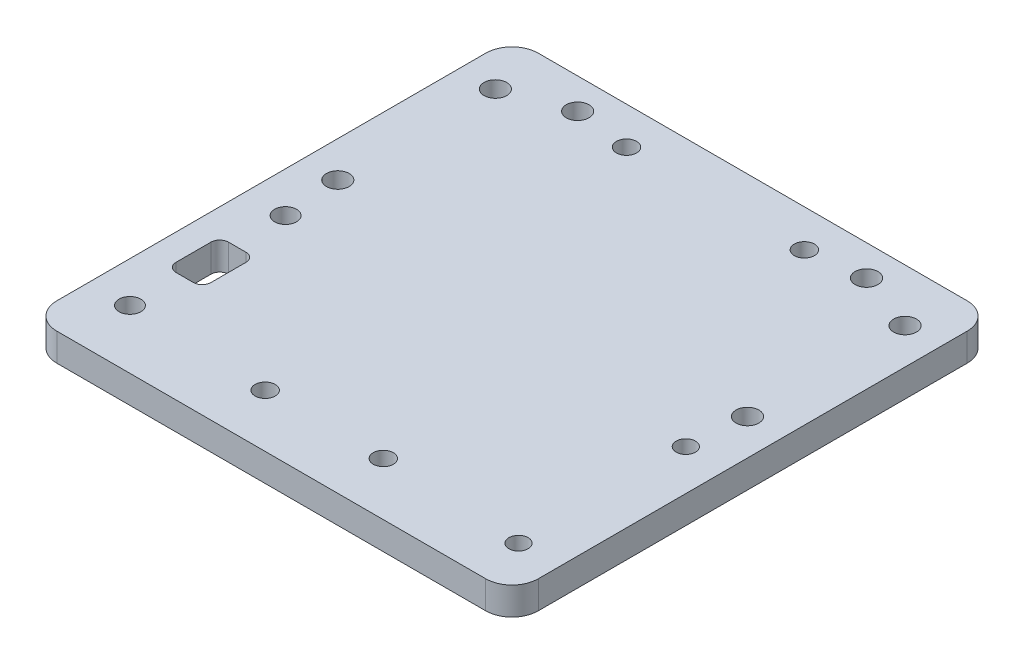
SolidWorks part; units mm, degrees
ref_plane "Front Plane" through (0, 0, 0) normal (0, 0, 1) x (1, 0, 0)
ref_plane "Top Plane" through (0, 0, 0) normal (0, 1, 0) x (1, 0, 0)
ref_plane "Right Plane" through (0, 0, 0) normal (1, 0, 0) x (0, 0, -1)
sketch "Sketch1" plane through (0, 0, 0) normal (0, 1, 0) x (1, 0, 0)
  line L1 (-27.5, 27.5) -> (27.5, 27.5)
  line L2 (-27.5, 27.5) -> (-27.5, -27.5)
  line L3 (-27.5, -27.5) -> (27.5, -27.5)
  line L4 (27.5, 27.5) -> (27.5, -27.5)
  line L5 (-27.5, 27.5) -> (27.5, -27.5) construction
  line L6 (-27.5, -27.5) -> (27.5, 27.5) construction
  point P0 (0, 0)
  dimension "D1" = 55
  dimension "D2" = 55
extrude "Boss-Extrude1" add sketch "Sketch1" along normal blind 3.175
sketch "Sketch2" plane through (0, 3.175, 0) normal (0, 1, 0) x (1, 0, 0)
  line L0 (0, 27.5) -> (0, -27.5) construction
  line L1 (27.5, 27.5) -> (-27.5, 27.5) construction
  line L2 (-27.5, -27.5) -> (27.5, -27.5) construction
  line L3 (-27.5, 27.5) -> (-27.5, -27.5) construction
  circle A0 centre (-23.4, 21.5) radius 1.3
  circle A1 centre (-23.4, 3.5) radius 1.3
  circle A2 centre (23.4, 3.5) radius 1.3
  circle A3 centre (23.4, 21.5) radius 1.3
  point P11 (-22.1, 21.5)
  point P17 (22.1, 21.5)
  dimension "D1" = 2.6
  dimension "D2" = 18
  dimension "D3" = 5.4
  dimension "D4" = 6
extrude "Cut-Extrude1" cut sketch "Sketch2" against normal up to surface (3.175 mm away) up to face at (0, 0, 0)
fillet "Fillet1" radius 3 4 edges at (-27.5, 1.5875, 27.5) (27.5, 1.5875, 27.5) (27.5, 1.5875, -27.5) (-27.5, 1.5875, -27.5)
sketch "Sketch3" plane through (0, 3.175, 0) normal (0, 1, 0) x (1, 0, 0)
  line L0 (-27.5, 0) -> (27.5, 0) construction
  line L1 (-22.865, -3) -> (22.855, -3) construction
  line L2 (-22.865, -3) -> (-22.865, -20.78) construction
  line L3 (-22.865, -20.78) -> (22.855, -22.11) construction
  line L4 (22.855, -3) -> (22.855, -22.11) construction
  line L5 (-27.5, 24.5) -> (-27.5, -24.5) construction
  line L6 (27.5, -24.5) -> (27.5, 24.5) construction
  circle A0 centre (-22.865, -3) radius 1.25
  circle A1 centre (22.855, -3) radius 1.1
  circle A2 centre (22.855, -22.11) radius 1.1
  circle A3 centre (-22.865, -20.78) radius 1.25
  dimension "D1" = 2.5
  dimension "D6" = 2.2
  dimension "D2" = 45.72
  dimension "D3" = 17.78
  dimension "D4" = 19.11
  dimension "D5" = 45.72
  dimension "D7" = 3
extrude "Cut-Extrude2" cut sketch "Sketch3" against normal up to surface (3.175 mm away) up to face at (23.4, 0, -20.2)
sketch "Sketch4" plane through (0, 3.175, 0) normal (0, 1, 0) x (1, 0, 0)
  line L0 (24.5, 27.5) -> (-24.5, 27.5) construction
  line L1 (-10.16, 23.24) -> (10.16, 23.24) construction
  line L2 (-10.16, 23.24) -> (-10.16, 8) construction
  line L3 (-10.16, 8) -> (10.16, 8) construction
  line L4 (10.16, 23.24) -> (10.16, 8) construction
  line L5 (-10.16, 23.24) -> (10.16, 8) construction
  line L6 (-10.16, 8) -> (10.16, 23.24) construction
  line L7 (0, 27.5) -> (0, -27.5) construction
  line L8 (-24.5, -27.5) -> (24.5, -27.5) construction
  circle A0 centre (-10.16, 23.24) radius 1.15
  circle A1 centre (10.16, 23.24) radius 1.15
  point P0 (0, 15.62)
  dimension "D1" = 2.3
  dimension "D2" = 20.32
  dimension "D3" = 15.24
  dimension "D4" = 8
extrude "Cut-Extrude3" cut sketch "Sketch4" against normal up to surface (3.175 mm away) up to face at (-22.865, 0, 22.03)
sketch "Sketch5" plane through (0, 3.175, 0) normal (0, 1, 0) x (1, 0, 0)
  line L0 (0, 27.5) -> (0, -27.5) construction
  line L1 (24.5, 27.5) -> (-24.5, 27.5) construction
  line L2 (-24.5, -27.5) -> (24.5, -27.5) construction
  circle A0 centre (-6.75, -21.45) radius 1.15
  circle A1 centre (6.75, -21.45) radius 1.15
  dimension "D1" = 2.3
  dimension "D2" = 6.75
  dimension "D3" = 6.05
extrude "Cut-Extrude4" cut sketch "Sketch5" against normal up to surface (3.175 mm away) up to face at (-10.16, 0, -22.09)
sketch "Sketch6" plane through (0, 3.175, 0) normal (0, 1, 0) x (1, 0, 0)
  line L0 (0, 27.5) -> (0, -27.5) construction
  line L1 (24.5, 27.5) -> (-24.5, 27.5) construction
  line L2 (-24.5, -27.5) -> (24.5, -27.5) construction
  circle A0 centre (-16.5, 24) radius 1.3
  circle A1 centre (16.5, 24) radius 1.3
  dimension "D1" = 2.6
  dimension "D2" = 16.5
  dimension "D3" = 3.5
extrude "Cut-Extrude5" cut sketch "Sketch6" against normal up to surface (3.175 mm away) up to face at (-6.75, 0, 22.6)
sketch "Sketch7" plane through (0, 3.175, 0) normal (0, 1, 0) x (1, 0, 0)
  line L0 (-27.5, 24.5) -> (-27.5, -24.5) construction
  line L1 (-23.5, -8.89) -> (-21.5, -8.89)
  line L2 (-24.5, -9.89) -> (-24.5, -13.89)
  line L3 (-23.5, -14.89) -> (-21.5, -14.89)
  line L4 (-20.5, -9.89) -> (-20.5, -13.89)
  line L5 (-24.5, -8.89) -> (-20.5, -14.89) construction
  line L6 (-24.5, -14.89) -> (-20.5, -8.89) construction
  circle A0 centre (-22.865, -3) radius 1.25 construction
  circle A1 centre (-22.865, -20.78) radius 1.25 construction
  arc A2 (-24.5, -13.89) -> (-23.5, -14.89) centre (-23.5, -13.89) ccw
  arc A3 (-21.5, -14.89) -> (-20.5, -13.89) centre (-21.5, -13.89) ccw
  arc A4 (-21.5, -8.89) -> (-20.5, -9.89) centre (-21.5, -9.89) cw
  arc A5 (-23.5, -8.89) -> (-24.5, -9.89) centre (-23.5, -9.89) ccw
  point P0 (-22.5, -11.89)
  point P7 (-22.2085, -12)
  dimension "D3" = 5.89
  dimension "D4" = 5.89
  dimension "D6" = 1
  dimension "D1" = 6
  dimension "D2" = 4
  dimension "D5" = 3
extrude "Cut-Extrude6" cut sketch "Sketch7" against normal up to surface (3.175 mm away) up to face at (-16.5, 0, -22.7)
